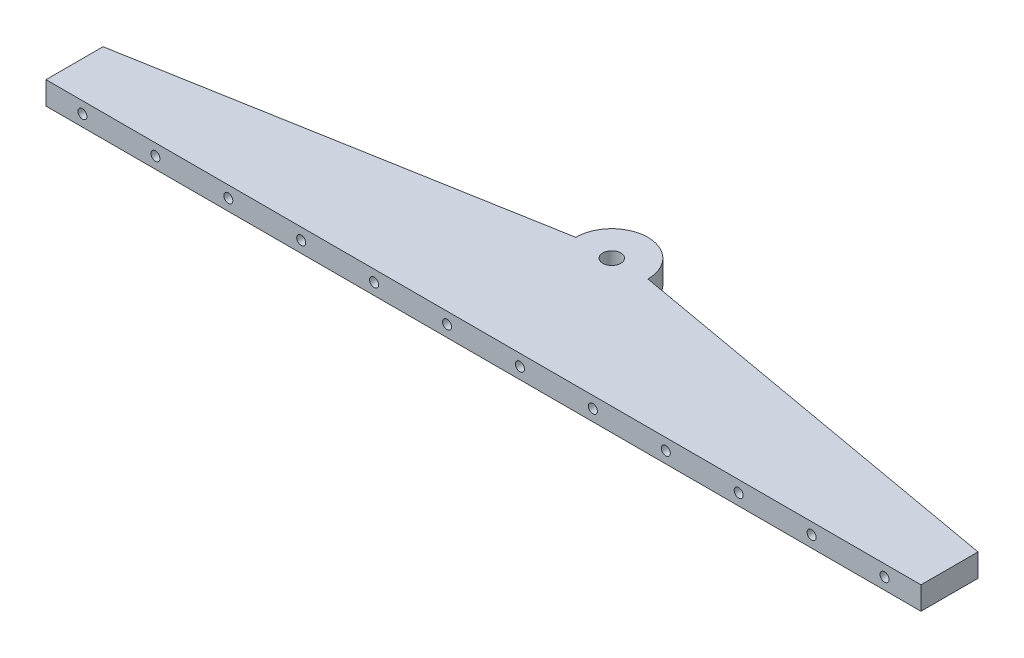
SolidWorks part; units mm, degrees
material "6063-T1"
ref_plane "Front" through (0, 0, 0) normal (0, 0, 1) x (1, 0, 0)
ref_plane "Top" through (0, 0, 0) normal (0, 1, 0) x (1, 0, 0)
ref_plane "Right" through (0, 0, 0) normal (1, 0, 0) x (0, 0, -1)
sketch "Sketch1" plane through (0, 0, 0) normal (0, 1, 0) x (1, 0, 0)
  line L1 (0, 0) -> (242.4, 0)
  line L2 (0, 0) -> (0, 71.1)
  line L3 (0, 71.1) -> (242.4, 71.1)
  line L4 (242.4, 0) -> (242.4, 71.1)
  dimension "D1" = 71.1
  dimension "D2" = 242.4
extrude "Boss-Extrude1" add sketch "Sketch1" along normal blind 6.35
sketch "Sketch2" plane through (0, 6.35, 0) normal (0, 1, 0) x (1, 0, 0)
  line L0 (0, 0) -> (0, 15.7961)
  line L1 (0, 71.1) -> (0, 0) construction
  line L2 (0, 15.7961) -> (111.2, 35.55)
  line L3 (242.4, 71.1) -> (0, 71.1) construction
  line L4 (131.2, 35.55) -> (242.4, 15.7961)
  line L5 (242.4, 0) -> (242.4, 71.1) construction
  line L6 (242.4, 15.7961) -> (242.4, 0)
  line L7 (242.4, 0) -> (0, 0)
  arc A0 (111.2, 35.55) -> (131.2, 35.55) centre (121.2, 35.55) cw
  point P10 (121.2, 71.1)
  point P11 (121.2, 35.55)
  point P17 (111.2, 35.55)
  point P18 (0, 0)
  point P19 (121.2, 35.55)
  point P21 (0, 35.55)
  dimension "D1" = 10
extrude "Cut-Extrude1" cut sketch "Sketch2" against normal blind 10 flip side to cut
hole_wizard "Tap Drill for M3x0.5 Tap1" positions "Sketch3" profile "Sketch4" hole size "M3x0.5" standard "ANSI Metric"
sketch "Sketch3" plane through (0, 0, 0) normal (0, 0, 1) x (1, 0, 0)
  line L0 (0, 3.175) -> (242.4, 3.175) construction
  line L1 (0, 6.35) -> (0, 0) construction
  line L2 (242.4, 6.35) -> (242.4, 0) construction
  point P9 (10.1, 3.175)
  point P15 (30.3, 3.175)
  point P16 (50.5, 3.175)
  point P17 (70.7, 3.175)
  point P18 (90.9, 3.175)
  point P19 (111.1, 3.175)
  point P20 (131.3, 3.175)
  point P21 (151.5, 3.175)
  point P22 (171.7, 3.175)
  point P23 (191.9, 3.175)
  point P24 (212.1, 3.175)
  point P25 (232.3, 3.175)
  dimension "D2" = 10.1
  dimension "D1" = 12
sketch "Sketch4" plane through (232.3, 3.175, 0) normal (1, 0, 0) x (0, -1, 0)
  line L0 (0, 0) -> (0, 6.7511)
  line L1 (0, 6.7511) -> (1.25, 6)
  line L2 (1.25, 6) -> (1.25, 0)
  line L5 (1.25, 0) -> (0, 0)
  line L10 (0, 6.7511) -> (-1.25, 6) construction
  line L11 (0, -6.35) -> (0, 107.95) construction
  dimension "Hole Dia." = 2.5
  dimension "Hole Depth" = 6
  dimension "Drill Angle" = 118
hole_wizard "Tap Drill for M3x0.5 Tap2" positions "Sketch5" profile "Sketch6" hole size "M3x0.5" standard "ANSI Metric"
sketch "Sketch5" plane through (0, 0, -71.1) normal (0, 0, -1) x (-1, 0, 0)
  line L0 (-242.4, 3.175) -> (0, 3.175) construction
  line L1 (-242.4, 6.35) -> (-242.4, 0) construction
  line L2 (0, 6.35) -> (0, 0) construction
  point P11 (-232.3, 3.175)
  point P17 (-212.1, 3.175)
  point P18 (-191.9, 3.175)
  point P19 (-171.7, 3.175)
  point P20 (-151.5, 3.175)
  point P21 (-131.3, 3.175)
  point P22 (-111.1, 3.175)
  point P23 (-90.9, 3.175)
  point P24 (-70.7, 3.175)
  point P25 (-50.5, 3.175)
  point P26 (-30.3, 3.175)
  point P27 (-10.1, 3.175)
  dimension "D1" = 10.1
  dimension "D2" = 12
sketch "Sketch6" plane through (10.1, 3.175, -71.1) normal (1, 0, 0) x (0, 1, 0)
  line L0 (0, 0) -> (0, 6.7511)
  line L1 (0, 6.7511) -> (1.25, 6)
  line L2 (1.25, 6) -> (1.25, 0)
  line L5 (1.25, 0) -> (0, 0)
  line L10 (0, 6.7511) -> (-1.25, 6) construction
  line L11 (0, -6.35) -> (0, 107.95) construction
  dimension "Hole Dia." = 2.5
  dimension "Hole Depth" = 6
  dimension "Drill Angle" = 118
hole_wizard "Tap Drill for M6x1.0 Tap1" positions "Sketch7" profile "Sketch8" hole size "M6x1.0" standard "ANSI Metric" end condition through all
sketch "Sketch7" plane through (0, 6.35, 0) normal (0, 1, 0) x (1, 0, 0)
  point P0 (121.2, 35.55)
sketch "Sketch8" plane through (121.2, 6.35, -35.55) normal (1, 0, 0) x (0, 0, 1)
  line L0 (0, 0) -> (0, 6.35)
  line L1 (0, 6.35) -> (2.5, 6.35)
  line L2 (2.5, 6.35) -> (2.5, 0)
  line L5 (2.5, 0) -> (0, 0)
  line L11 (0, -6.35) -> (0, 107.95) construction
  dimension "Thru Hole Dia." = 5
  dimension "Thru Hole Depth" = 6.35
